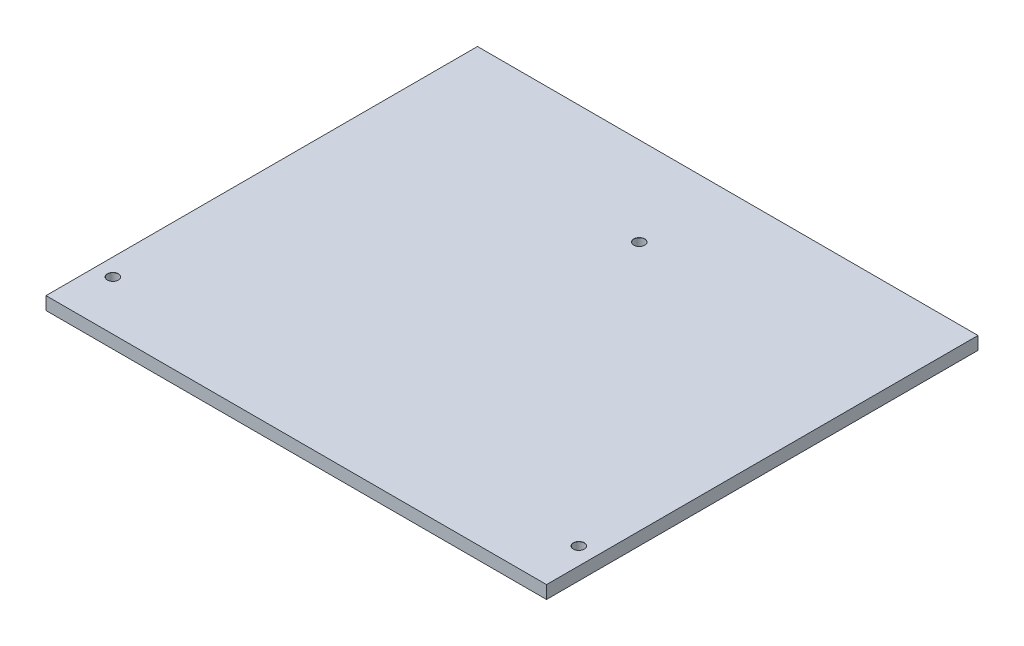
SolidWorks part; units mm, degrees
ref_plane "Front Plane" through (0, 0, 0) normal (0, 0, 1) x (1, 0, 0)
ref_plane "Top Plane" through (0, 0, 0) normal (0, 1, 0) x (1, 0, 0)
ref_plane "Right Plane" through (0, 0, 0) normal (1, 0, 0) x (0, 0, -1)
sketch "Sketch1" plane through (0, 0, 0) normal (0, 1, 0) x (1, 0, 0)
  line L1 (-58, -50) -> (58, -50)
  line L2 (-58, -50) -> (-58, 50)
  line L3 (-58, 50) -> (58, 50)
  line L4 (58, -50) -> (58, 50)
  line L5 (-58, -50) -> (58, 50) construction
  line L6 (-58, 50) -> (58, -50) construction
  point P0 (0, 0)
  dimension "D1" = 100
  dimension "D2" = 116
extrude "Boss-Extrude1" add sketch "Sketch1" along normal blind 3
sketch "Sketch2" plane through (0, 3, 0) normal (0, 1, 0) x (1, 0, 0)
  line L0 (-58, 50) -> (-58, -50) construction
  line L1 (58, -50) -> (58, 50) construction
  line L2 (-58, -50) -> (58, -50) construction
  line L4 (58, 50) -> (-58, 50) construction
  point P0 (-54, -38.5)
  point P1 (54, -38.5)
  point P2 (0, 0)
  point P9 (0, 29.5)
  point P10 (0, 0)
  dimension "D1" = 4
  dimension "D2" = 4
  dimension "D3" = 11.5
  dimension "D4" = 20.5
hole_wizard "Tap Drill for M3 Tap1" positions "Sketch3" profile "Sketch4" hole size "M3" standard "ISO" end condition through all
sketch "Sketch3" plane through (0, 3, 0) normal (0, 1, 0) x (1, 0, 0)
  point P0 (0, 29.5)
  point P3 (-54, -38.5)
  point P6 (54, -38.5)
sketch "Sketch4" plane through (0, 3, -29.5) normal (1, 0, 0) x (0, 0, 1)
  line L0 (0, 0) -> (0, 3)
  line L1 (0, 3) -> (1.25, 3)
  line L2 (1.25, 3) -> (1.25, 0.025)
  line L3 (1.25, 0.025) -> (1.275, 0)
  line L5 (1.275, 0) -> (0, 0)
  line L6 (-1.25, 0.025) -> (-1.275, 0) construction
  line L11 (0, -6.35) -> (0, 107.95) construction
  dimension "Thru Hole Dia." = 2.5
  dimension "Thru Hole Depth" = 3
  dimension "Near C'Sink Dia." = 2.55
  dimension "Near C'Sink Angle" = 90
